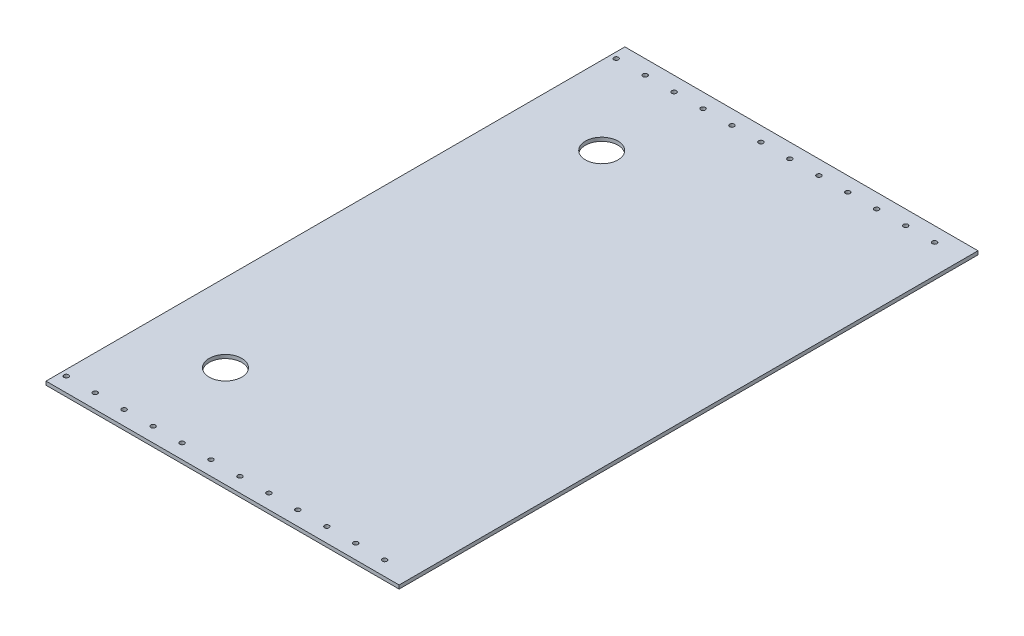
SolidWorks part; units mm, degrees
material "Lexan"
ref_plane "Front Plane" through (0, 0, 0) normal (0, 0, 1) x (1, 0, 0)
ref_plane "Top Plane" through (0, 0, 0) normal (0, 1, 0) x (1, 0, 0)
ref_plane "Right Plane" through (0, 0, 0) normal (1, 0, 0) x (0, 0, -1)
sketch "Sketch1" plane through (0, 0, 0) normal (0, 1, 0) x (1, 0, 0)
  line L1 (0, 0) -> (571.5, 0)
  line L2 (0, 0) -> (0, 508)
  line L3 (0, 508) -> (571.5, 508)
  line L4 (571.5, 0) -> (571.5, 508)
  dimension "D1" = 571.5
  dimension "D2" = 508
extrude "Boss-Extrude1" add sketch "Sketch1" along normal blind 3.175
sketch "Sketch2" plane through (0, 3.175, 0) normal (0, 1, 0) x (1, 0, 0)
  line L0 (273.05, 419.1) -> (273.05, 508) construction
  line L1 (215.9, 419.1) -> (330.2, 419.1) construction
  line L3 (215.9, 88.9) -> (330.2, 88.9) construction
  line L4 (571.5, 0) -> (571.5, 508) construction
  line L5 (571.5, 508) -> (0, 508) construction
  line L6 (273.05, 88.9) -> (273.05, 0) construction
  line L7 (0, 0) -> (571.5, 0) construction
  circle A1 centre (330.2, 419.1) radius 14.2875
  circle A3 centre (330.2, 88.9) radius 14.2875
  dimension "D1" = 114.3
  dimension "D2" = 28.575
  dimension "D3" = 241.3
  dimension "D4" = 28.575
  dimension "D7" = 330.2
  dimension "D8" = 241.3
extrude "Cut-Extrude1" cut sketch "Sketch2" against normal blind 3.175
sketch "Sketch4" plane through (0, 3.175, 0) normal (0, 1, 0) x (1, 0, 0)
  line L0 (571.5, 495.3) -> (0, 495.3) construction
  line L1 (571.5, 0) -> (571.5, 508) construction
  line L2 (0, 508) -> (0, 0) construction
  line L3 (571.5, 508) -> (0, 508) construction
  line L4 (0, 254) -> (571.5, 254) construction
  line L5 (571.5, 12.7) -> (0, 12.7) construction
  circle A0 centre (546.1, 495.3) radius 2.0193
  circle A1 centre (520.7, 495.3) radius 2.0193
  circle A2 centre (495.3, 495.3) radius 2.0193
  circle A3 centre (469.9, 495.3) radius 2.0193
  circle A4 centre (444.5, 495.3) radius 2.0193
  circle A5 centre (419.1, 495.3) radius 2.0193
  circle A6 centre (393.7, 495.3) radius 2.0193
  circle A7 centre (368.3, 495.3) radius 2.0193
  circle A8 centre (342.9, 495.3) radius 2.0193
  circle A9 centre (317.5, 495.3) radius 2.0193
  circle A10 centre (292.1, 495.3) radius 2.0193
  circle A11 centre (266.7, 495.3) radius 2.0193
  circle A12 centre (228.6, 495.3) radius 2.0193
  circle A13 centre (203.2, 495.3) radius 2.0193
  circle A14 centre (203.2, 12.7) radius 2.0193
  circle A15 centre (228.6, 12.7) radius 2.0193
  circle A16 centre (266.7, 12.7) radius 2.0193
  circle A17 centre (292.1, 12.7) radius 2.0193
  circle A18 centre (317.5, 12.7) radius 2.0193
  circle A19 centre (342.9, 12.7) radius 2.0193
  circle A20 centre (368.3, 12.7) radius 2.0193
  circle A21 centre (393.7, 12.7) radius 2.0193
  circle A22 centre (419.1, 12.7) radius 2.0193
  circle A23 centre (444.5, 12.7) radius 2.0193
  circle A24 centre (469.9, 12.7) radius 2.0193
  circle A25 centre (495.3, 12.7) radius 2.0193
  circle A26 centre (520.7, 12.7) radius 2.0193
  circle A27 centre (546.1, 12.7) radius 2.0193
  dimension "D2" = 4.0386
  dimension "D3" = 25.4
  dimension "D5" = 38.1
  dimension "D6" = 25.4
  dimension "D1" = 12.7
  dimension "D4" = 12
extrude "Cut-Extrude3" cut sketch "Sketch4" against normal through all both
sketch "Sketch5" plane through (0, 0, 0) normal (-1, 0, 0) x (0, 0, 1)
  line L1 (-567.431, 71.2281) -> (52.1486, 71.2281)
  line L2 (-567.431, 71.2281) -> (-567.431, -17.807)
  line L3 (-567.431, -17.807) -> (52.1486, -17.807)
  line L4 (52.1486, 71.2281) -> (52.1486, -17.807)
extrude "Cut-Extrude4" cut sketch "Sketch5" against normal blind 165.1
sketch "Sketch6" plane through (165.1, 0, 0) normal (-1, 0, 0) x (0, 0, 1)
  line L1 (-508, 3.175) -> (0, 3.175)
  line L2 (-508, 3.175) -> (-508, 0)
  line L3 (-508, 0) -> (0, 0)
  line L4 (0, 3.175) -> (0, 0)
extrude "Cut-Extrude5" cut sketch "Sketch6" against normal blind 96.52
